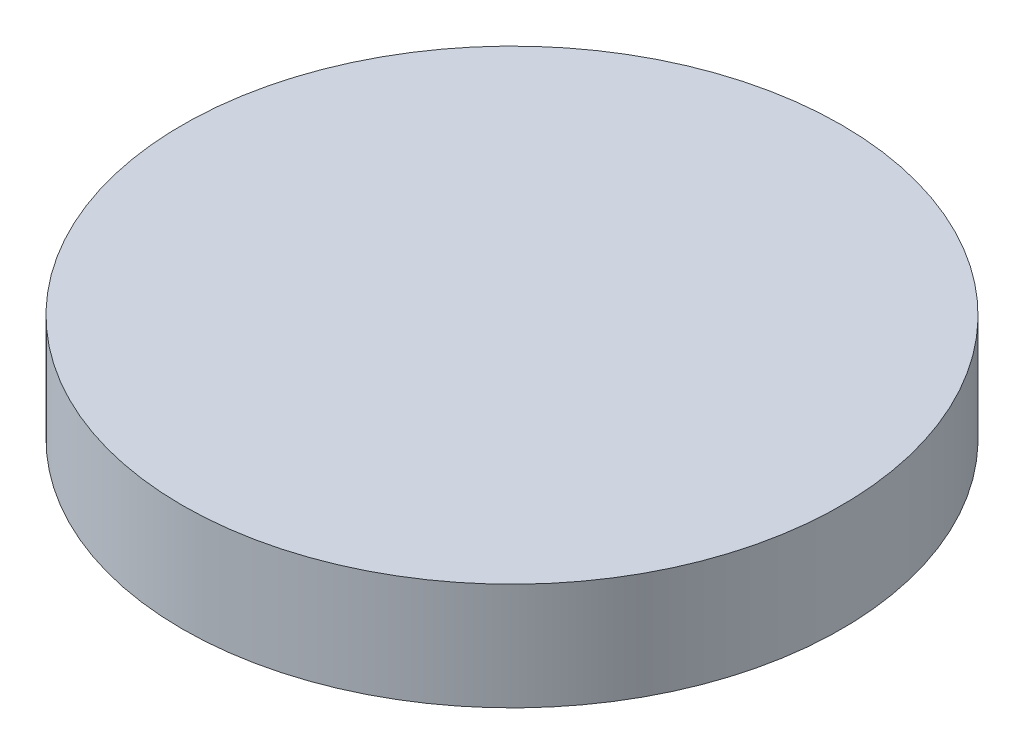
SolidWorks part; units mm, degrees
ref_plane "Front Plane" through (0, 0, 0) normal (0, 0, 1) x (1, 0, 0)
ref_plane "Top Plane" through (0, 0, 0) normal (0, 1, 0) x (1, 0, 0)
ref_plane "Right Plane" through (0, 0, 0) normal (1, 0, 0) x (0, 0, -1)
sketch "Sketch1" plane through (0, 0, 0) normal (0, 1, 0) x (1, 0, 0)
  circle A0 centre (0, 0) radius 40
extrude "Boss-Extrude1" add sketch "Sketch1" along normal blind 13
